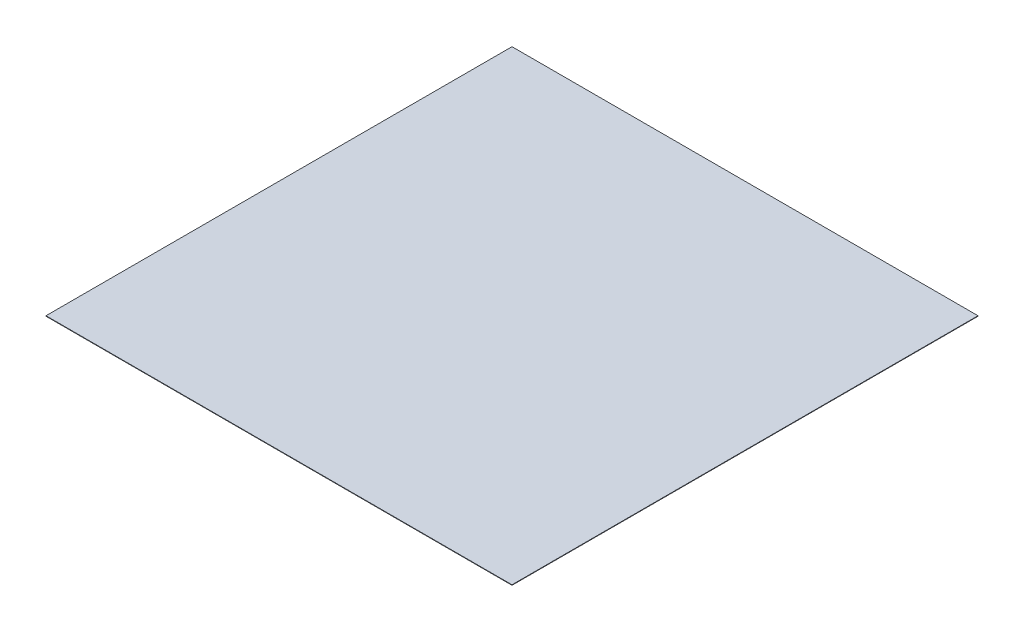
SolidWorks part; units mm, degrees
ref_plane "Front Plane" through (0, 0, 0) normal (0, 0, 1) x (1, 0, 0)
ref_plane "Top Plane" through (0, 0, 0) normal (0, 1, 0) x (1, 0, 0)
ref_plane "Right Plane" through (0, 0, 0) normal (1, 0, 0) x (0, 0, -1)
sketch "Sketch1" plane through (0, 0, 0) normal (0, 0, 1) x (1, 0, 0)
  line L0 (0, 0) -> (1000, 0)
  line L1 (1000, 0) -> (1000, 1)
  line L2 (1000, 1) -> (0, 1)
  line L3 (0, 1) -> (0, 0)
  dimension "D1" = 1000
  dimension "D2" = 1
extrude "Boss-Extrude1" add sketch "Sketch1" along normal blind 1000
